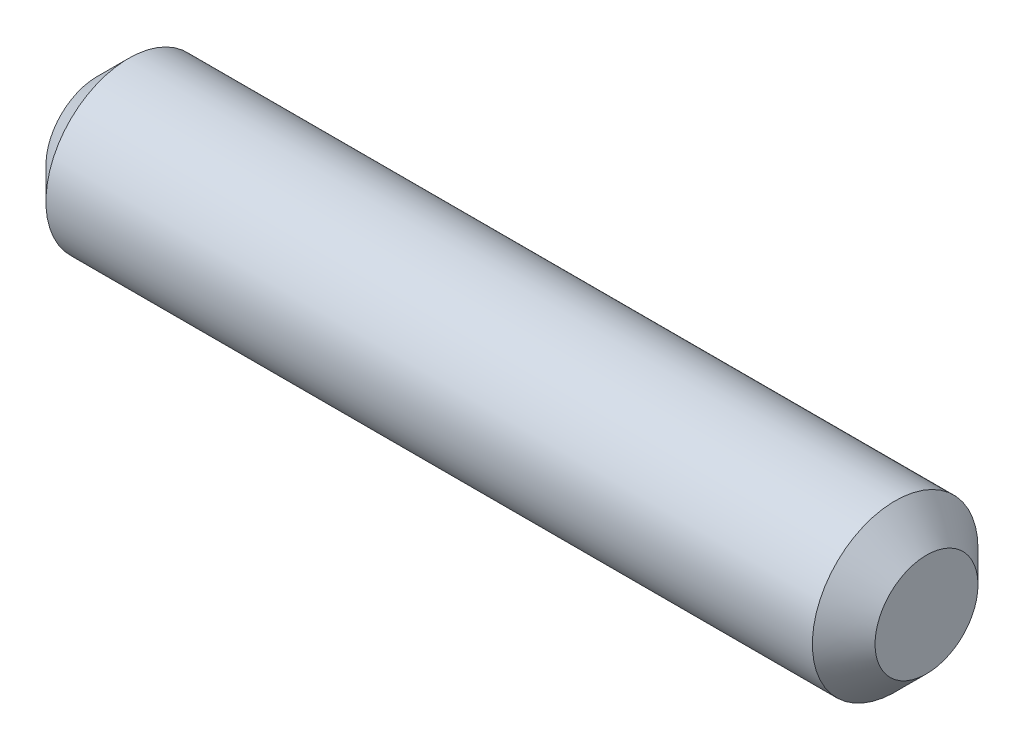
SolidWorks part; units mm, degrees
ref_plane "Front Plane" through (0, 0, 0) normal (0, 0, 1) x (1, 0, 0)
ref_plane "Top Plane" through (0, 0, 0) normal (0, 1, 0) x (1, 0, 0)
ref_plane "Right Plane" through (0, 0, 0) normal (1, 0, 0) x (0, 0, -1)
sketch "Sketch1" plane through (0, 0, 0) normal (1, 0, 0) x (0, 0, -1)
  circle A0 centre (0, 0) radius 1.585
  dimension "D1" = 3.17
extrude "Boss-Extrude1" add sketch "Sketch1" along normal mid plane 15.87
chamfer "Chamfer1" distance 0.6 angle 45 2 edges at (-7.935, 0, -1.585) (7.935, 0, -1.585)
